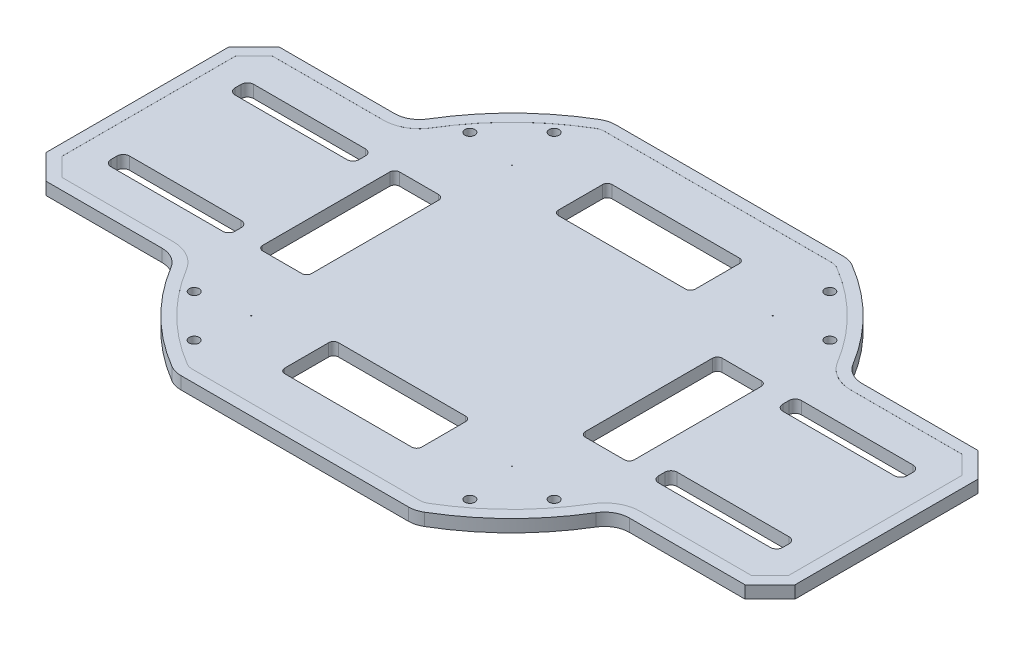
SolidWorks part; units mm, degrees
ref_plane "Front Plane" through (0, 0, 0) normal (0, 0, 1) x (1, 0, 0)
ref_plane "Top Plane" through (0, 0, 0) normal (0, 1, 0) x (1, 0, 0)
ref_plane "Right Plane" through (0, 0, 0) normal (1, 0, 0) x (0, 0, -1)
sketch "Sketch1" plane through (0, 0, 0) normal (0, 1, 0) x (1, 0, 0)
  line L0 (0, -1000) -> (0, 49000) construction
  line L1 (-23.2448, 44.45) -> (23.2448, 44.45)
  line L2 (-76.5969, 18.7325) -> (-76.5969, -18.7325)
  line L3 (-23.2448, -44.45) -> (23.2448, -44.45)
  line L4 (76.5969, 18.7325) -> (76.5969, -18.7325)
  line L6 (35.4178, 36.4243) -> (41.9684, 29.8736) construction
  line L7 (-76.5969, 0) -> (76.5969, 0) construction
  line L8 (-71.5169, 23.8125) -> (-47.8309, 23.8125)
  line L9 (-71.5169, -23.8125) -> (-47.8309, -23.8125)
  line L10 (-23.8125, 64.7529) -> (-23.8125, -44.45) construction
  line L11 (23.8125, 64.7529) -> (23.8125, -44.45) construction
  line L12 (47.8309, -23.8125) -> (71.5169, -23.8125)
  line L13 (47.8309, 23.8125) -> (71.5169, 23.8125)
  line L14 (-76.5969, -18.7325) -> (-71.5169, -23.8125)
  line L15 (-71.5169, 23.8125) -> (-76.5969, 18.7325)
  line L16 (71.5169, 23.8125) -> (76.5969, 18.7325)
  line L17 (71.5169, -23.8125) -> (76.5969, -18.7325)
  line L18 (707.1068, -707.1068) -> (-34648.2323, 34648.2323) construction
  line L19 (-707.1068, -707.1068) -> (34648.2323, 34648.2323) construction
  circle A0 centre (0, 0) radius 6.35 construction
  arc A1 (-25.8276, 43.7444) -> (-43.4827, 26.2659) centre (0, 0) ccw
  arc A2 (25.8276, 43.7444) -> (23.2448, 44.45) centre (23.2448, 39.37) ccw
  arc A3 (-23.2448, 44.45) -> (-25.8276, 43.7444) centre (-23.2448, 39.37) ccw
  arc A4 (25.8276, -43.7444) -> (43.4827, -26.2659) centre (0, 0) ccw
  arc A5 (25.8276, -43.7444) -> (23.2448, -44.45) centre (23.2448, -39.37) cw
  arc A6 (-25.8276, -43.7444) -> (-23.2448, -44.45) centre (-23.2448, -39.37) ccw
  arc A7 (-43.4827, -26.2659) -> (-25.8276, -43.7444) centre (0, 0) ccw
  arc A8 (43.4827, 26.2659) -> (25.8276, 43.7444) centre (0, 0) ccw
  arc A9 (-47.8309, -23.8125) -> (-43.4827, -26.2659) centre (-47.8309, -28.8925) cw
  arc A10 (47.8309, -23.8125) -> (43.4827, -26.2659) centre (47.8309, -28.8925) ccw
  arc A11 (43.4827, 26.2659) -> (47.8309, 23.8125) centre (47.8309, 28.8925) ccw
  arc A12 (-47.8309, 23.8125) -> (-43.4827, 26.2659) centre (-47.8309, 28.8925) ccw
  circle A13 centre (36.8191, 28.198) radius 1.016
  circle A14 centre (28.198, 36.8191) radius 1.016
  circle A15 centre (26.6716, 26.6716) radius 0.081
  circle A16 centre (26.6716, -26.6716) radius 0.081
  circle A17 centre (36.8191, -28.198) radius 1.016
  circle A18 centre (28.198, -36.8191) radius 1.016
  circle A19 centre (-26.6716, -26.6716) radius 0.081
  circle A20 centre (-28.198, -36.8191) radius 1.016
  circle A21 centre (-36.8191, -28.198) radius 1.016
  circle A22 centre (-26.6716, 26.6716) radius 0.081
  circle A23 centre (-36.8191, 28.198) radius 1.016
  circle A24 centre (-28.198, 36.8191) radius 1.016
  point P0 (0, 0)
  point P8 (76.5969, -23.8125)
  point P11 (-76.5969, -23.8125)
  point P12 (-76.5969, 23.8125)
  point P34 (76.5969, 23.8125)
  point P81 (0, 0)
  dimension "D3" = 12.7
  dimension "D6" = 5.08
  dimension "D1" = 5.08
  dimension "D2" = 5.08
  dimension "D7" = 4.826
  dimension "D4" = 23.8125
  dimension "D5" = 23.8125
  dimension "D8" = 6.096
  dimension "D13" = 4
extrude "Boss-Extrude1" add sketch "Sketch1" along normal blind 2.54
sketch "Sketch3" plane through (0, 2.54, 0) normal (0, 1, 0) x (1, 0, 0)
  line L0 (0, -61.6163) -> (0, 61.6163) construction
  line L1 (-109.9353, 0) -> (109.9353, 0) construction
  line L2 (-14, -28) -> (14, -28) construction
  line L3 (-14, 33.5) -> (14, 33.5)
  line L4 (-14, 33.5) -> (-14, 22.5)
  line L5 (-14, 22.5) -> (14, 22.5)
  line L6 (14, 33.5) -> (14, 22.5)
  line L7 (0, 22.5) -> (0, 33.5) construction
  line L8 (-14, 28) -> (14, 28) construction
  line L9 (0, -22.5) -> (0, -33.5) construction
  line L10 (14, -33.5) -> (14, -22.5)
  line L11 (-14, -22.5) -> (14, -22.5)
  line L12 (-14, -33.5) -> (-14, -22.5)
  line L13 (-14, -33.5) -> (14, -33.5)
  line L14 (38, 0) -> (28, 0) construction
  line L15 (-38, -14) -> (-28, -14)
  line L16 (-38, -14) -> (-38, 14)
  line L17 (-38, 14) -> (-28, 14)
  line L18 (-28, -14) -> (-28, 14)
  line L19 (-33, 14) -> (-33, -14) construction
  line L20 (-38, 0) -> (-28, 0) construction
  line L21 (33, 14) -> (33, -14) construction
  line L22 (28, -14) -> (28, 14)
  line L23 (38, 14) -> (28, 14)
  line L24 (38, -14) -> (38, 14)
  line L25 (38, -14) -> (28, -14)
  point P0 (0, 28)
  point P4 (0, 0)
  point P7 (0, 0)
  point P19 (0, -28)
  point P20 (-33, 0)
  point P32 (33, 0)
  dimension "D1" = 28
  dimension "D2" = 11
  dimension "D3" = 22.5
  dimension "D4" = 10
  dimension "D5" = 28
  dimension "D6" = 28
sketch "Sketch4" plane through (0, 2.54, 0) normal (0, 1, 0) x (1, 0, 0)
  line L0 (-1000, 0) -> (49000, 0) construction
  line L1 (76.5969, -18.7325) -> (76.5969, 18.7325) construction
  line L2 (44.5929, 14.605) -> (67.4529, 14.605)
  line L3 (43.3229, 13.335) -> (43.3229, 12.065)
  line L4 (44.5929, 10.795) -> (67.4529, 10.795)
  line L5 (68.7229, 13.335) -> (68.7229, 12.065)
  line L6 (43.3229, 14.605) -> (68.7229, 10.795) construction
  line L7 (43.3229, 10.795) -> (68.7229, 14.605) construction
  line L8 (68.7229, -13.335) -> (68.7229, -12.065)
  line L9 (44.5929, -10.795) -> (67.4529, -10.795)
  line L10 (43.3229, -13.335) -> (43.3229, -12.065)
  line L11 (44.5929, -14.605) -> (67.4529, -14.605)
  line L12 (0, 0) -> (0, -50000) construction
  line L13 (-44.5929, -14.605) -> (-67.4529, -14.605)
  line L14 (-43.3229, -13.335) -> (-43.3229, -12.065)
  line L15 (-44.5929, -10.795) -> (-67.4529, -10.795)
  line L16 (-68.7229, -13.335) -> (-68.7229, -12.065)
  line L17 (-43.3229, 10.795) -> (-68.7229, 14.605) construction
  line L18 (-43.3229, 14.605) -> (-68.7229, 10.795) construction
  line L19 (-68.7229, 13.335) -> (-68.7229, 12.065)
  line L20 (-44.5929, 10.795) -> (-67.4529, 10.795)
  line L21 (-43.3229, 13.335) -> (-43.3229, 12.065)
  line L22 (-44.5929, 14.605) -> (-67.4529, 14.605)
  arc A0 (44.5929, 10.795) -> (43.3229, 12.065) centre (44.5929, 12.065) cw
  arc A1 (43.3229, 13.335) -> (44.5929, 14.605) centre (44.5929, 13.335) cw
  arc A2 (68.7229, 12.065) -> (67.4529, 10.795) centre (67.4529, 12.065) cw
  arc A3 (68.7229, 13.335) -> (67.4529, 14.605) centre (67.4529, 13.335) ccw
  arc A4 (68.7229, -12.065) -> (67.4529, -10.795) centre (67.4529, -12.065) ccw
  arc A5 (68.7229, -13.335) -> (67.4529, -14.605) centre (67.4529, -13.335) cw
  arc A6 (44.5929, -10.795) -> (43.3229, -12.065) centre (44.5929, -12.065) ccw
  arc A7 (43.3229, -13.335) -> (44.5929, -14.605) centre (44.5929, -13.335) ccw
  arc A8 (-43.3229, -13.335) -> (-44.5929, -14.605) centre (-44.5929, -13.335) cw
  arc A9 (-44.5929, -10.795) -> (-43.3229, -12.065) centre (-44.5929, -12.065) cw
  arc A10 (-68.7229, -13.335) -> (-67.4529, -14.605) centre (-67.4529, -13.335) ccw
  arc A11 (-68.7229, -12.065) -> (-67.4529, -10.795) centre (-67.4529, -12.065) cw
  arc A12 (-68.7229, 13.335) -> (-67.4529, 14.605) centre (-67.4529, 13.335) cw
  arc A13 (-68.7229, 12.065) -> (-67.4529, 10.795) centre (-67.4529, 12.065) ccw
  arc A14 (-43.3229, 13.335) -> (-44.5929, 14.605) centre (-44.5929, 13.335) ccw
  arc A15 (-44.5929, 10.795) -> (-43.3229, 12.065) centre (-44.5929, 12.065) ccw
  point P1 (56.0229, 12.7)
  point P64 (-56.0229, 12.7)
  dimension "D5" = 1.27
  dimension "D1" = 25.4
  dimension "D2" = 3.81
  dimension "D3" = 7.874
  dimension "D4" = 10.795
extrude "切除-拉伸1" cut sketch "Sketch3" against normal blind 10
extrude "Cut-Extrude2" cut sketch "Sketch4" against normal blind 2.54
fillet "圆角1" radius 1 16 edges at (14, 1.27, 33.5) (-14, 1.27, 33.5) (-14, 1.27, 22.5) (-28, 1.27, 14) (-38, 1.27, 14) (-28, 1.27, -14) (-38, 1.27, -14) (14, 1.27, -33.5) (14, 1.27, -22.5) (-14, 1.27, -22.5) (-14, 1.27, -33.5) (38, 1.27, -14) (38, 1.27, 14) (28, 1.27, -14) (28, 1.27, 14) (14, 1.27, 22.5)
sketch "Sketch8" plane through (0, 2.54, 0) normal (0, 1, 0) x (1, 0, 0)
  line L12 (47.8309, -23.8125) -> (71.5169, -23.8125)
  line L13 (71.5169, -23.8125) -> (76.5969, -18.7325)
  line L14 (76.5969, -18.7325) -> (76.5969, 18.7325)
  line L15 (76.5969, 18.7325) -> (71.5169, 23.8125)
  line L16 (71.5169, 23.8125) -> (47.8309, 23.8125)
  line L17 (23.2448, 44.45) -> (-23.2448, 44.45)
  line L18 (-47.8309, 23.8125) -> (-71.5169, 23.8125)
  line L19 (-71.5169, 23.8125) -> (-76.5969, 18.7325)
  line L20 (-76.5969, 18.7325) -> (-76.5969, -18.7325)
  line L21 (-76.5969, -18.7325) -> (-71.5169, -23.8125)
  line L22 (-71.5169, -23.8125) -> (-47.8309, -23.8125)
  line L23 (-23.2448, -44.45) -> (23.2448, -44.45)
  line L24 (47.8309, -21.5125) -> (70.5642, -21.5125)
  line L25 (70.5642, -21.5125) -> (74.2969, -17.7798)
  line L26 (74.2969, -17.7798) -> (74.2969, 17.7798)
  line L27 (74.2969, 17.7798) -> (70.5642, 21.5125)
  line L28 (70.5642, 21.5125) -> (47.8309, 21.5125)
  line L29 (23.2448, 42.15) -> (-23.2448, 42.15)
  line L30 (-47.8309, 21.5125) -> (-70.5642, 21.5125)
  line L31 (-70.5642, 21.5125) -> (-74.2969, 17.7798)
  line L32 (-74.2969, 17.7798) -> (-74.2969, -17.7798)
  line L33 (-74.2969, -17.7798) -> (-70.5642, -21.5125)
  line L34 (-70.5642, -21.5125) -> (-47.8309, -21.5125)
  line L35 (-23.2448, -42.15) -> (23.2448, -42.15)
  line L36 (47.8309, -21.5125) -> (70.5642, -21.5125)
  line L37 (70.5642, -21.5125) -> (74.2969, -17.7798)
  line L38 (74.2969, -17.7798) -> (74.2969, 17.7798)
  line L39 (74.2969, 17.7798) -> (70.5642, 21.5125)
  line L40 (70.5642, 21.5125) -> (47.8309, 21.5125)
  line L41 (23.2448, 42.15) -> (-23.2448, 42.15)
  line L42 (-47.8309, 21.5125) -> (-70.5642, 21.5125)
  line L43 (-70.5642, 21.5125) -> (-74.2969, 17.7798)
  line L44 (-74.2969, 17.7798) -> (-74.2969, -17.7798)
  line L45 (-74.2969, -17.7798) -> (-70.5642, -21.5125)
  line L46 (-70.5642, -21.5125) -> (-47.8309, -21.5125)
  line L47 (-23.2448, -42.15) -> (23.2448, -42.15)
  arc A12 (23.2448, -44.45) -> (25.8276, -43.7444) centre (23.2448, -39.37) ccw
  arc A13 (25.8276, -43.7444) -> (43.4827, -26.2659) centre (0, 0) ccw
  arc A14 (47.8309, -23.8125) -> (43.4827, -26.2659) centre (47.8309, -28.8925) ccw
  arc A15 (43.4827, 26.2659) -> (47.8309, 23.8125) centre (47.8309, 28.8925) ccw
  arc A16 (43.4827, 26.2659) -> (25.8276, 43.7444) centre (0, 0) ccw
  arc A17 (25.8276, 43.7444) -> (23.2448, 44.45) centre (23.2448, 39.37) ccw
  arc A18 (-23.2448, 44.45) -> (-25.8276, 43.7444) centre (-23.2448, 39.37) ccw
  arc A19 (-25.8276, 43.7444) -> (-43.4827, 26.2659) centre (0, 0) ccw
  arc A20 (-47.8309, 23.8125) -> (-43.4827, 26.2659) centre (-47.8309, 28.8925) ccw
  arc A21 (-43.4827, -26.2659) -> (-47.8309, -23.8125) centre (-47.8309, -28.8925) ccw
  arc A22 (-43.4827, -26.2659) -> (-25.8276, -43.7444) centre (0, 0) ccw
  arc A23 (-25.8276, -43.7444) -> (-23.2448, -44.45) centre (-23.2448, -39.37) ccw
  arc A24 (23.2448, -42.15) -> (24.6582, -41.7639) centre (23.2448, -39.37) ccw
  arc A25 (24.6582, -41.7639) -> (41.514, -25.0767) centre (0, 0) ccw
  arc A26 (47.8309, -21.5125) -> (41.514, -25.0767) centre (47.8309, -28.8925) ccw
  arc A27 (41.514, 25.0767) -> (47.8309, 21.5125) centre (47.8309, 28.8925) ccw
  arc A28 (41.514, 25.0767) -> (24.6582, 41.7639) centre (0, 0) ccw
  arc A29 (24.6582, 41.7639) -> (23.2448, 42.15) centre (23.2448, 39.37) ccw
  arc A30 (-23.2448, 42.15) -> (-24.6582, 41.7639) centre (-23.2448, 39.37) ccw
  arc A31 (-24.6582, 41.7639) -> (-41.514, 25.0767) centre (0, 0) ccw
  arc A32 (-47.8309, 21.5125) -> (-41.514, 25.0767) centre (-47.8309, 28.8925) ccw
  arc A33 (-41.514, -25.0767) -> (-47.8309, -21.5125) centre (-47.8309, -28.8925) ccw
  arc A34 (-41.514, -25.0767) -> (-24.6582, -41.7639) centre (0, 0) ccw
  arc A35 (-24.6582, -41.7639) -> (-23.2448, -42.15) centre (-23.2448, -39.37) ccw
  arc A36 (23.2448, -42.15) -> (24.6582, -41.7639) centre (23.2448, -39.37) ccw
  arc A37 (24.6582, -41.7639) -> (41.514, -25.0767) centre (0, 0) ccw
  arc A38 (47.8309, -21.5125) -> (41.514, -25.0767) centre (47.8309, -28.8925) ccw
  arc A39 (41.514, 25.0767) -> (47.8309, 21.5125) centre (47.8309, 28.8925) ccw
  arc A40 (41.514, 25.0767) -> (24.6582, 41.7639) centre (0, 0) ccw
  arc A41 (24.6582, 41.7639) -> (23.2448, 42.15) centre (23.2448, 39.37) ccw
  arc A42 (-23.2448, 42.15) -> (-24.6582, 41.7639) centre (-23.2448, 39.37) ccw
  arc A43 (-24.6582, 41.7639) -> (-41.514, 25.0767) centre (0, 0) ccw
  arc A44 (-47.8309, 21.5125) -> (-41.514, 25.0767) centre (-47.8309, 28.8925) ccw
  arc A45 (-41.514, -25.0767) -> (-47.8309, -21.5125) centre (-47.8309, -28.8925) ccw
  arc A46 (-41.514, -25.0767) -> (-24.6582, -41.7639) centre (0, 0) ccw
  arc A47 (-24.6582, -41.7639) -> (-23.2448, -42.15) centre (-23.2448, -39.37) ccw
  dimension "D1" = 2.3
  dimension "D2" = 2.3
extrude "Boss-Extrude2" add sketch "Sketch8" along normal blind 0.01
